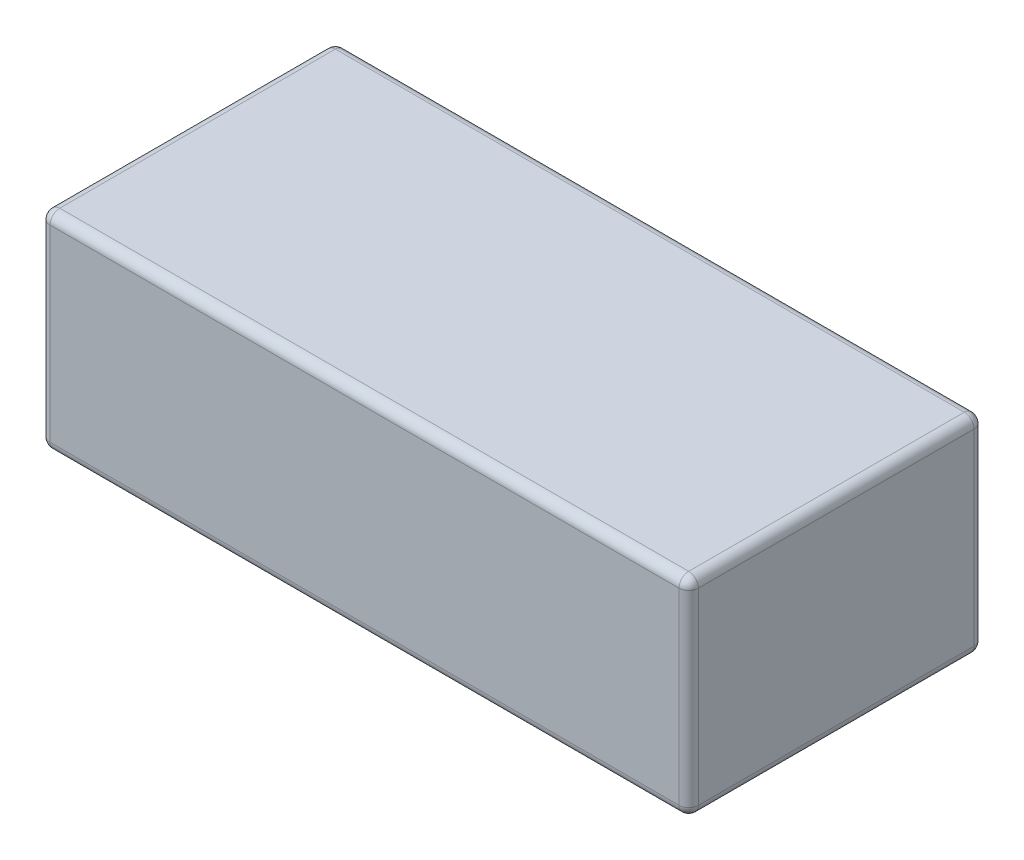
SolidWorks part; units mm, degrees
ref_plane "Front Plane" through (0, 0, 0) normal (0, 0, 1) x (1, 0, 0)
ref_plane "Top Plane" through (0, 0, 0) normal (0, 1, 0) x (1, 0, 0)
ref_plane "Right Plane" through (0, 0, 0) normal (1, 0, 0) x (0, 0, -1)
sketch "Sketch1" plane through (0, 0, 0) normal (0, 1, 0) x (1, 0, 0)
  line L1 (-100, -45.5) -> (100, -45.5)
  line L2 (-100, -45.5) -> (-100, 45.5)
  line L3 (-100, 45.5) -> (100, 45.5)
  line L4 (100, -45.5) -> (100, 45.5)
  line L5 (-100, -45.5) -> (100, 45.5) construction
  line L6 (-100, 45.5) -> (100, -45.5) construction
  point P0 (0, 0)
  dimension "D1" = 200
  dimension "D2" = 91
extrude "Boss-Extrude1" add sketch "Sketch1" along normal blind 64
fillet "Fillet1" radius 3 12 edges at (0, 0, -45.5) (100, 0, 0) (100, 32, -45.5) (-100, 32, -45.5) (-100, 0, 0) (0, 0, 45.5) (100, 32, 45.5) (-100, 32, 45.5) (0, 64, -45.5) (100, 64, 0) (0, 64, 45.5) (-100, 64, 0)
sketch "Bend-Lines15" [suppressed] plane through (0, 0, 0) normal (0, 1, 0) x (1, 0, 0)
sketch "Bounding-Box15" [suppressed] plane through (0, 0, 0) normal (0, 1, 0) x (1, 0, 0)
